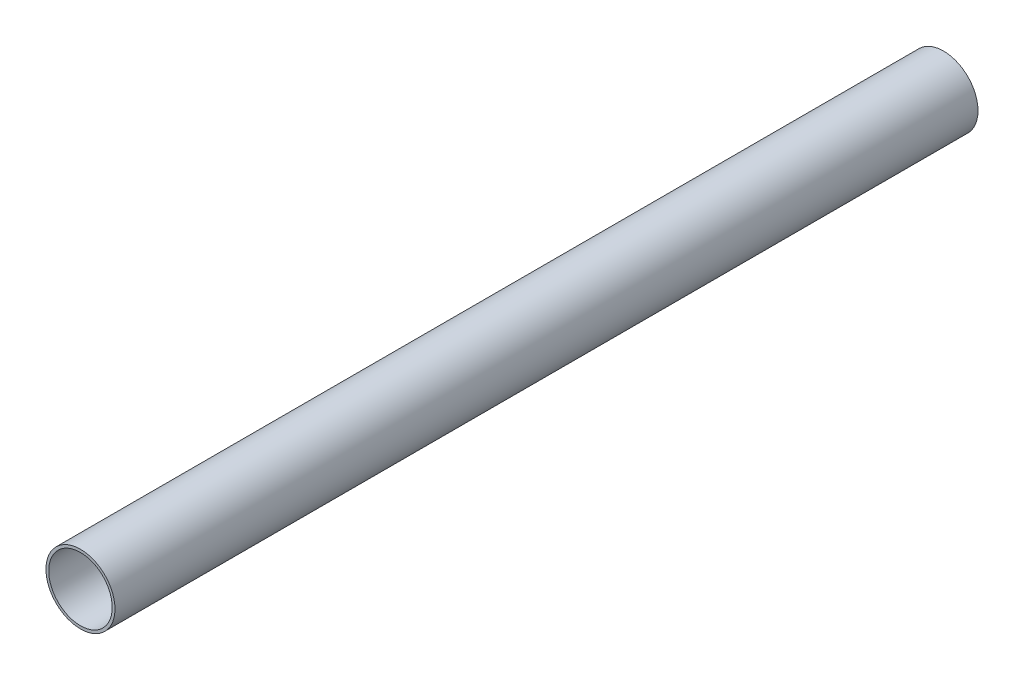
SolidWorks part; units mm, degrees
ref_plane "정면" through (0, 0, 0) normal (0, 0, 1) x (1, 0, 0)
ref_plane "윗면" through (0, 0, 0) normal (0, 1, 0) x (1, 0, 0)
ref_plane "우측면" through (0, 0, 0) normal (1, 0, 0) x (0, 0, -1)
sketch "스케치1" plane through (0, 0, 0) normal (0, 0, 1) x (1, 0, 0)
  circle A0 centre (0, 0) radius 20
extrude "돌출-얇게1" add sketch "스케치1" along normal blind 500 thin thin type one direction reverse wall 1.6
